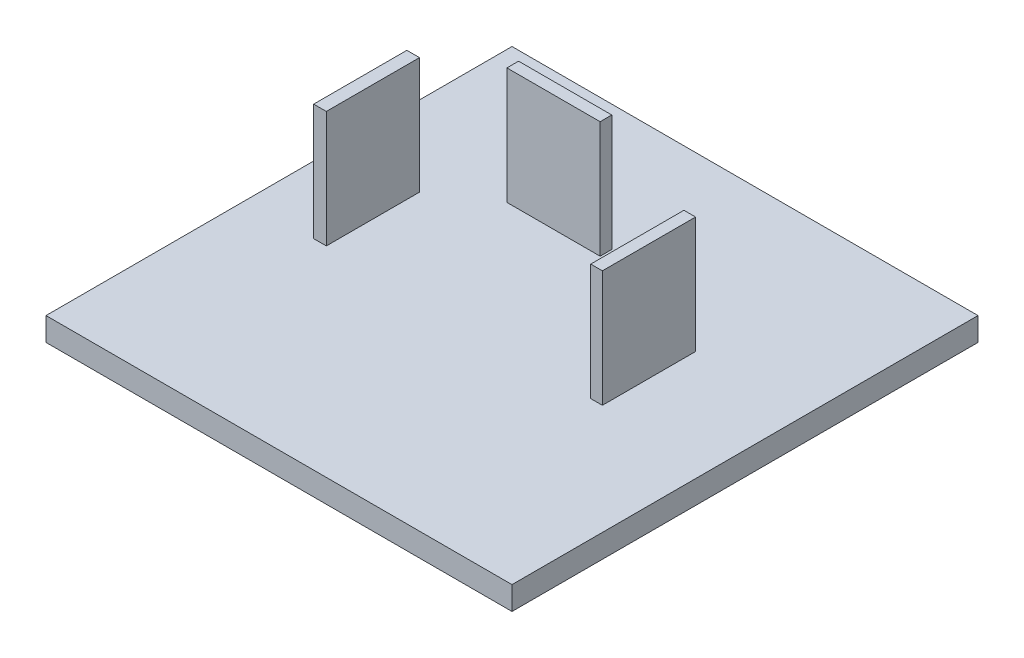
SolidWorks part; units mm, degrees
ref_plane "Front Plane" through (0, 0, 0) normal (0, 0, 1) x (1, 0, 0)
ref_plane "Top Plane" through (0, 0, 0) normal (0, 1, 0) x (1, 0, 0)
ref_plane "Right Plane" through (0, 0, 0) normal (1, 0, 0) x (0, 0, -1)
sketch "Sketch1" plane through (0, 0, 0) normal (0, 0, 1) x (1, 0, 0)
  line L1 (-143.9559, -25.0215) -> (-93.1559, -25.0215)
  line L2 (-143.9559, -25.0215) -> (-143.9559, -27.5615)
  line L3 (-143.9559, -27.5615) -> (-93.1559, -27.5615)
  line L4 (-93.1559, -25.0215) -> (-93.1559, -27.5615)
  dimension "D1" = 50.8
  dimension "D2" = 2.54
extrude "Boss-Extrude1" add sketch "Sketch1" along normal blind 50.8 contours L1 L4 L3 L2
sketch "Sketch2" plane through (0, -25.0215, 0) normal (0, 1, 0) x (1, 0, 0)
  line L1 (-119.3539, -14.9955) -> (-129.5139, -14.9955)
  line L2 (-119.3539, -14.9955) -> (-119.3539, -13.7255)
  line L3 (-119.3539, -13.7255) -> (-129.5139, -13.7255)
  line L4 (-129.5139, -14.9955) -> (-129.5139, -13.7255)
  line L5 (-106.4235, -18.7887) -> (-105.1535, -18.7887)
  line L6 (-106.4235, -18.7887) -> (-106.4235, -28.9487)
  line L7 (-106.4235, -28.9487) -> (-105.1535, -28.9487)
  line L8 (-105.1535, -18.7887) -> (-105.1535, -28.9487)
  line L9 (-136.6274, -18.7887) -> (-135.2479, -18.7887)
  line L10 (-136.6274, -18.7887) -> (-136.6274, -28.9487)
  line L11 (-136.6274, -28.9487) -> (-135.2479, -28.9487)
  line L12 (-135.2479, -18.7887) -> (-135.2479, -28.9487)
  dimension "D1" = 10.16
  dimension "D2" = 1.27
  dimension "D3" = 1.27
  dimension "D4" = 10.16
  dimension "D5" = 10.16
  dimension "D6" = 1.3795
extrude "Boss-Extrude2" add sketch "Sketch2" along normal blind 12.7
